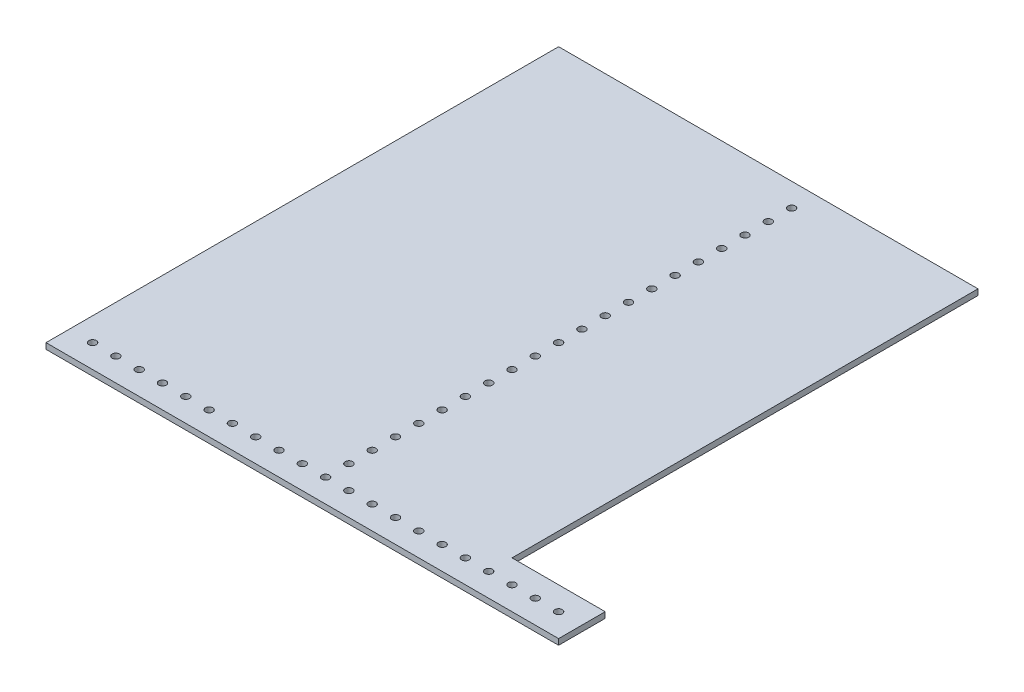
SolidWorks part; units mm, degrees
material "PC High Viscosity"
ref_plane "Front Plane" through (0, 0, 0) normal (0, 0, 1) x (1, 0, 0)
ref_plane "Top Plane" through (0, 0, 0) normal (0, 1, 0) x (1, 0, 0)
ref_plane "Right Plane" through (0, 0, 0) normal (1, 0, 0) x (0, 0, -1)
sketch "Sketch1" plane through (0, 0, 0) normal (0, 1, 0) x (1, 0, 0)
  line L0 (12.7, 12.7) -> (25.4, 12.7) construction
  line L1 (0, 0) -> (279.4, 0)
  line L2 (0, 0) -> (0, 279.4)
  line L3 (0, 279.4) -> (279.4, 279.4)
  line L4 (152.4, 0) -> (152.4, 279.4) construction
  line L5 (139.7, 12.7) -> (139.7, 25.4) construction
  line L6 (139.7, 38.1) -> (139.7, 50.8) construction
  line L7 (139.7, 12.7) -> (139.7, 0) construction
  line L8 (139.7, 0) -> (152.4, 0) construction
  line L9 (139.7, 266.7) -> (139.7, 279.4) construction
  line L10 (139.7, 279.4) -> (152.4, 279.4) construction
  line L11 (279.4, 0) -> (279.4, 279.4)
  circle A0 centre (12.7, 12.7) radius 2.0193
  circle A1 centre (25.4, 12.7) radius 2.0193
  circle A2 centre (38.1, 12.7) radius 2.0193
  circle A3 centre (50.8, 12.7) radius 2.0193
  circle A4 centre (63.5, 12.7) radius 2.0193
  circle A5 centre (76.2, 12.7) radius 2.0193
  circle A6 centre (88.9, 12.7) radius 2.0193
  circle A7 centre (101.6, 12.7) radius 2.0193
  circle A8 centre (114.3, 12.7) radius 2.0193
  circle A9 centre (127, 12.7) radius 2.0193
  circle A10 centre (139.7, 12.7) radius 2.0193
  circle A11 centre (139.7, 25.4) radius 2.0193
  circle A12 centre (139.7, 38.1) radius 2.0193
  circle A13 centre (139.7, 50.8) radius 2.0193
  circle A14 centre (139.7, 63.5) radius 2.0193
  circle A15 centre (139.7, 76.2) radius 2.0193
  circle A16 centre (139.7, 88.9) radius 2.0193
  circle A17 centre (139.7, 101.6) radius 2.0193
  circle A18 centre (139.7, 114.3) radius 2.0193
  circle A19 centre (139.7, 127) radius 2.0193
  circle A20 centre (139.7, 139.7) radius 2.0193
  circle A21 centre (139.7, 152.4) radius 2.0193
  circle A22 centre (139.7, 165.1) radius 2.0193
  circle A23 centre (139.7, 177.8) radius 2.0193
  circle A24 centre (139.7, 190.5) radius 2.0193
  circle A25 centre (139.7, 203.2) radius 2.0193
  circle A26 centre (139.7, 215.9) radius 2.0193
  circle A27 centre (139.7, 228.6) radius 2.0193
  circle A28 centre (139.7, 241.3) radius 2.0193
  circle A29 centre (139.7, 254) radius 2.0193
  circle A30 centre (139.7, 266.7) radius 2.0193
  circle A31 centre (152.4, 12.7) radius 2.0193
  circle A32 centre (165.1, 12.7) radius 2.0193
  circle A33 centre (177.8, 12.7) radius 2.0193
  circle A34 centre (190.5, 12.7) radius 2.0193
  circle A35 centre (203.2, 12.7) radius 2.0193
  circle A36 centre (215.9, 12.7) radius 2.0193
  circle A37 centre (228.6, 12.7) radius 2.0193
  circle A38 centre (241.3, 12.7) radius 2.0193
  circle A39 centre (254, 12.7) radius 2.0193
  circle A40 centre (266.7, 12.7) radius 2.0193
  dimension "D3" = 12.7
  dimension "D4" = 12.7
  dimension "D5" = 4.0386
  dimension "D1" = 279.4
  dimension "D2" = 152.4
  dimension "D7" = 12.7
  dimension "D9" = 12.7
  dimension "D6" = 11
  dimension "D8" = 21
extrude "Boss-Extrude1" add sketch "Sketch1" along normal blind 3.175
sketch "Sketch2" plane through (0, 3.175, 0) normal (0, 1, 0) x (1, 0, 0)
  line L0 (279.4, 25.4) -> (228.6, 25.4)
  line L1 (279.4, 0) -> (279.4, 279.4) construction
  line L2 (0, 0) -> (279.4, 0) construction
  line L3 (228.6, 25.4) -> (228.6, 279.4)
  line L4 (279.4, 279.4) -> (0, 279.4) construction
  line L5 (228.6, 279.4) -> (279.4, 279.4)
  line L6 (279.4, 279.4) -> (279.4, 25.4)
  dimension "D1" = 25.4
  dimension "D2" = 50.8
extrude "Cut-Extrude1" cut sketch "Sketch2" against normal through all
